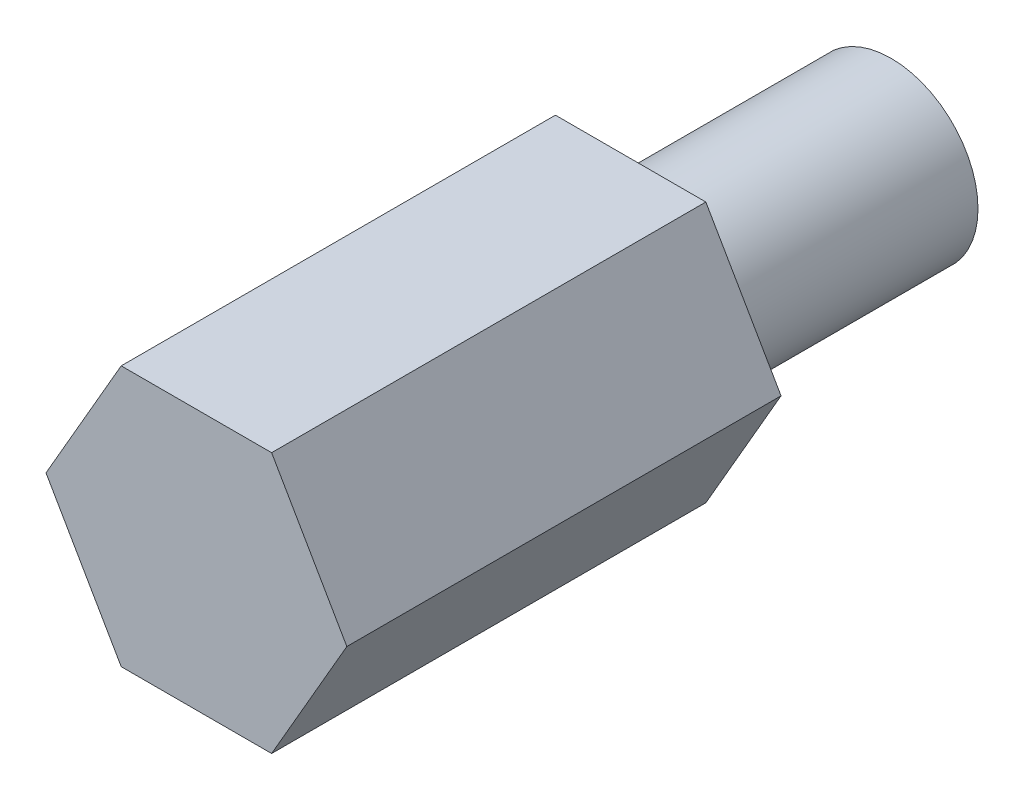
SolidWorks part; units mm, degrees
material "黄铜"
ref_plane "前视基准面" through (0, 0, 0) normal (0, 0, 1) x (1, 0, 0)
ref_plane "上视基准面" through (0, 0, 0) normal (0, 1, 0) x (1, 0, 0)
ref_plane "右视基准面" through (0, 0, 0) normal (1, 0, 0) x (0, 0, -1)
other "Configuration Table"
sketch "草图2" plane through (0, 0, 0) normal (0, 0, 1) x (1, 0, 0)
  line L1 (1.7321, 0) -> (0.866, 1.5)
  line L2 (0.866, 1.5) -> (-0.866, 1.5)
  line L3 (-0.866, 1.5) -> (-1.7321, 0)
  line L4 (-1.7321, 0) -> (-0.866, -1.5)
  line L5 (-0.866, -1.5) -> (0.866, -1.5)
  line L6 (0.866, -1.5) -> (1.7321, 0)
  circle A0 centre (0, 0) radius 1.5 construction
  dimension "D1" = 3
extrude "凸台-拉伸1" add sketch "草图2" along normal blind 5
sketch "草图3" plane through (0, 0, 0) normal (0, 0, -1) x (-1, 0, 0)
  circle A0 centre (0, 0) radius 1
  dimension "D1" = 2
extrude "凸台-拉伸2" add sketch "草图3" along normal blind 3
